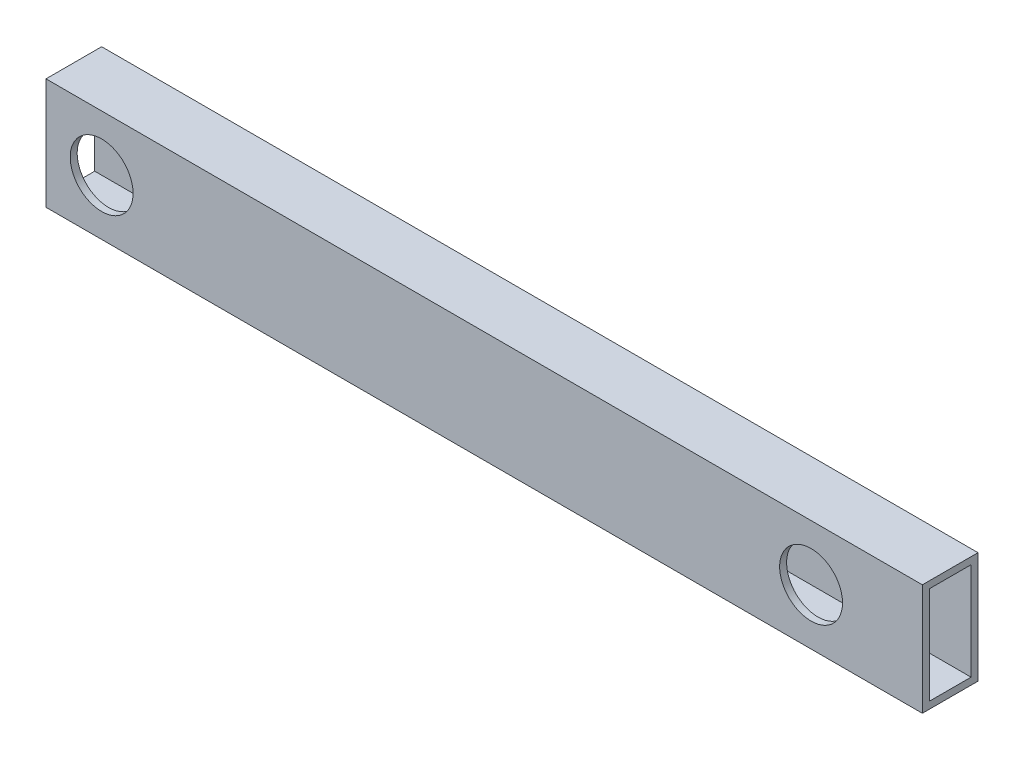
SolidWorks part; units mm, degrees
ref_plane "Front Plane" through (0, 0, 0) normal (0, 0, 1) x (1, 0, 0)
ref_plane "Top Plane" through (0, 0, 0) normal (0, 1, 0) x (1, 0, 0)
ref_plane "Right Plane" through (0, 0, 0) normal (1, 0, 0) x (0, 0, -1)
sketch "Sketch1" plane through (0, 0, 0) normal (1, 0, 0) x (0, 0, -1)
  line L1 (0, 0) -> (25.4, 0)
  line L2 (0, 0) -> (0, 50.8)
  line L3 (0, 50.8) -> (25.4, 50.8)
  line L4 (25.4, 0) -> (25.4, 50.8)
  line L5 (3.175, 3.175) -> (22.225, 3.175)
  line L6 (3.175, 3.175) -> (3.175, 47.625)
  line L7 (3.175, 47.625) -> (22.225, 47.625)
  line L8 (22.225, 3.175) -> (22.225, 47.625)
  dimension "D1" = 3.175
  dimension "D2" = 3.175
  dimension "D3" = 3.175
  dimension "D4" = 3.175
  dimension "D5" = 25.4
  dimension "D6" = 50.8
extrude "Boss-Extrude1" add sketch "Sketch1" along normal blind 400.05
sketch "Sketch2" plane through (0, 0, 0) normal (0, 0, 1) x (1, 0, 0)
  line L0 (400.05, 50.8) -> (0, 50.8) construction
  line L1 (400.05, 50.8) -> (400.05, 0) construction
  line L2 (0, 50.8) -> (0, 0) construction
  circle A0 centre (349.25, 25.4) radius 14.351
  circle A1 centre (25.4, 25.4) radius 14.351
  dimension "D1" = 25.4
  dimension "D2" = 25.4
  dimension "D3" = 50.8
  dimension "D4" = 25.4
  dimension "D5" = 28.702
  dimension "D6" = 28.702
extrude "Cut-Extrude1" cut sketch "Sketch2" against normal up to surface (25.4 mm away) up to face at (200.025, 25.4, -25.4)
